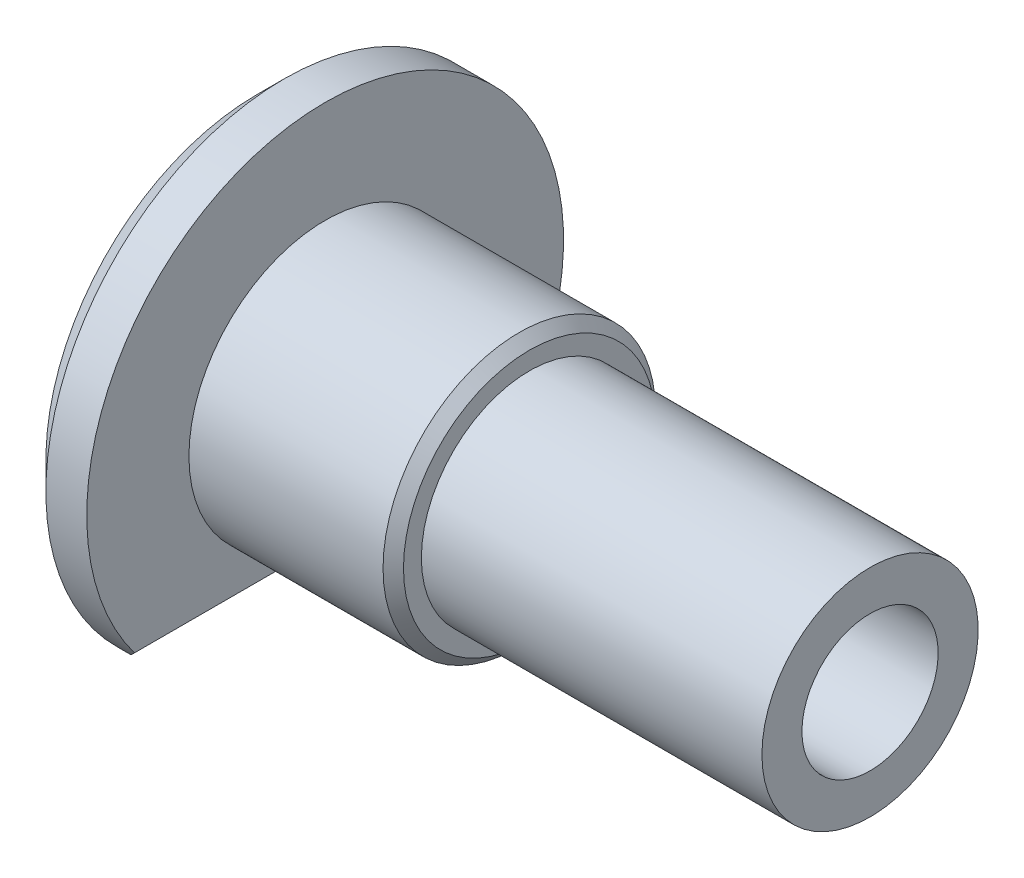
SolidWorks part; units mm, degrees
ref_plane "Спереди" through (0, 0, 0) normal (0, 0, 1) x (1, 0, 0)
ref_plane "Сверху" through (0, 0, 0) normal (0, 1, 0) x (1, 0, 0)
ref_plane "Справа" through (0, 0, 0) normal (1, 0, 0) x (0, 0, -1)
sketch "Эскиз1" plane through (0, 0, 0) normal (0, 1, 0) x (1, 0, 0)
  line L0 (0, 0) -> (25.136, 0) construction
  line L1 (0, 2) -> (18, 2)
  line L2 (18, 2) -> (18, 3.175)
  line L3 (18, 3.175) -> (8, 3.175)
  line L4 (2, 7) -> (2, 4)
  line L5 (2, 7) -> (0, 7)
  line L6 (0, 7) -> (0, 2)
  line L7 (2, 4) -> (7.7, 4)
  line L8 (8, 3.7) -> (8, 3.175)
  line L9 (7.7, 4) -> (8, 3.7)
  point P3 (0, 2)
  point P11 (8, 4)
  dimension "D1" = 6.35
  dimension "D2" = 4
  dimension "D3" = 14
  dimension "D4" = 2
  dimension "D5" = 6
  dimension "D6" = 8
  dimension "D7" = 10
  dimension "D10" = 0.3
revolve "Повернуть1" add sketch "Эскиз1" angle 360 about L0
cosmetic thread "Условное изображение резьбы1" parameters "D1"=4, "D2"=6.891
sketch "Эскиз2" plane through (0, 0, 0) normal (-1, 0, 0) x (0, 0, 1)
  line L0 (-4.899, -5) -> (4.899, -5)
  circle A0 centre (0, 0) radius 7 construction
  circle A1 centre (0, 0) radius 2 construction
  circle M2 centre (0, 0) radius 7
  dimension "D1" = 5
extrude "Вырез-Вытянуть2" cut sketch "Эскиз2" against normal through all contours L0 M2
chamfer "Фаска1" distance 0.8 angle 45 3 edges at (2, -5, 0) (2, 7, 0) (0, 7, 0)
